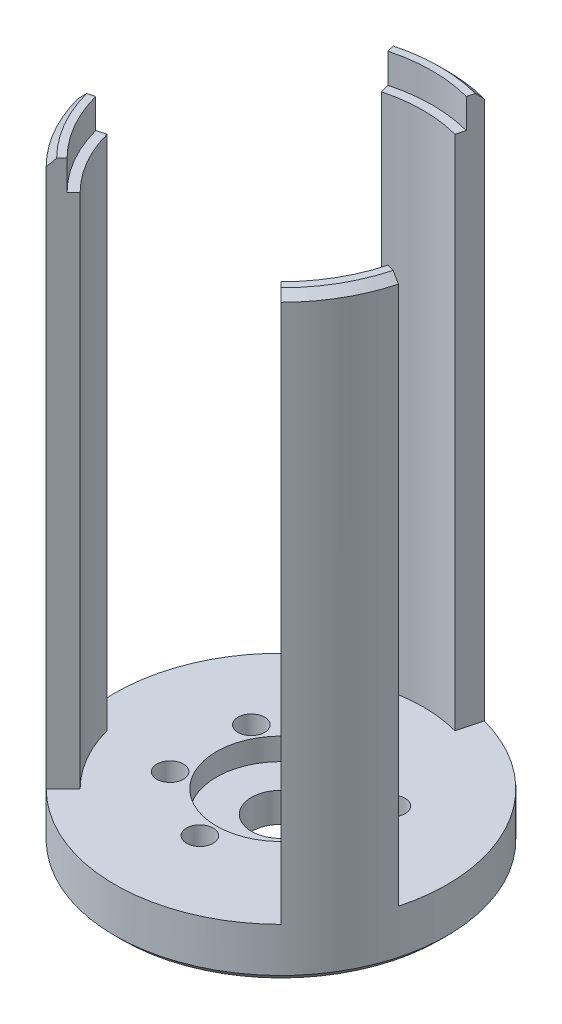
SolidWorks part; units mm, degrees
ref_plane "Front Plane" through (0, 0, 0) normal (0, 0, 1) x (1, 0, 0)
ref_plane "Top Plane" through (0, 0, 0) normal (0, 1, 0) x (1, 0, 0)
ref_plane "Right Plane" through (0, 0, 0) normal (1, 0, 0) x (0, 0, -1)
sketch "Sketch1" plane through (0, 0, 0) normal (0, 1, 0) x (1, 0, 0)
  line L0 (0, 0) -> (0, 11) construction
  line L1 (0, 0) -> (9.5263, 5.5) construction
  circle A0 centre (0, 0) radius 22.5
  circle A1 centre (0, 0) radius 11 construction
  circle A2 centre (0, 11) radius 1.8
  circle A3 centre (9.5263, 5.5) radius 1.8
  circle A4 centre (9.5263, -5.5) radius 1.8
  circle A5 centre (0, -11) radius 1.8
  circle A6 centre (-9.5263, -5.5) radius 1.8
  circle A7 centre (-9.5263, 5.5) radius 1.8
  circle A8 centre (0, 0) radius 4
  dimension "D1" = 45
  dimension "D2" = 22
  dimension "D3" = 3.6
  dimension "D5" = 8
  dimension "D4" = 60
extrude "Boss-Extrude1" add sketch "Sketch1" along normal blind 7
sketch "Sketch4" plane through (0, 7, 0) normal (0, 1, 0) x (1, 0, 0)
  circle A0 centre (0, 0) radius 8.75
  dimension "D1" = 17.5
extrude "Cut-Extrude2" cut sketch "Sketch4" against normal blind 3
sketch "Sketch6" plane through (0, 0, 0) normal (0, -1, 0) x (1, 0, 0)
  circle A0 centre (0, 11) radius 3.25
  circle A1 centre (9.5263, -5.5) radius 3.25
  circle A2 centre (-9.5263, -5.5) radius 3.25
  point P9 (0, 0)
  dimension "D1" = 6.5
  dimension "D2" = 3
extrude "Cut-Extrude3" cut sketch "Sketch6" against normal blind 2.5
sketch "Sketch2" plane through (0, 7, 0) normal (0, 1, 0) x (1, 0, 0)
  line L0 (0, 0) -> (0, 22.5) construction
  line L1 (0, 0) -> (9.5263, -5.5) construction
  line L2 (9.5263, -5.5) -> (19.4856, -11.25) construction
  line L3 (0, 0) -> (-9.5263, -5.5) construction
  line L4 (-9.5263, -5.5) -> (-19.4856, -11.25) construction
  line L5 (4.9823, 18.5941) -> (5.8234, 21.7333)
  line L6 (-4.9823, 18.5941) -> (-5.8234, 21.7333)
  line L7 (18.5941, -4.9823) -> (21.7333, -5.8234)
  line L8 (13.6118, -13.6118) -> (15.9099, -15.9099)
  line L9 (-13.6118, -13.6118) -> (-15.9099, -15.9099)
  line L10 (-18.5941, -4.9823) -> (-21.7333, -5.8234)
  circle A0 centre (0, 0) radius 22.5 construction
  arc A2 (15.9099, -15.9099) -> (21.7333, -5.8234) centre (0, 0) ccw
  arc A4 (5.8234, 21.7333) -> (-5.8234, 21.7333) centre (0, 0) ccw
  arc A5 (4.9823, 18.5941) -> (-4.9823, 18.5941) centre (0, 0) ccw
  arc A6 (13.6118, -13.6118) -> (18.5941, -4.9823) centre (0, 0) ccw
  arc A7 (-21.7333, -5.8234) -> (-15.9099, -15.9099) centre (0, 0) ccw
  arc A8 (-18.5941, -4.9823) -> (-13.6118, -13.6118) centre (0, 0) ccw
  point P26 (0, 0)
  dimension "D1" = 19.25
  dimension "D2" = 15
  dimension "D3" = 3
extrude "Boss-Extrude2" add sketch "Sketch2" along normal blind 74
sketch "Sketch7" plane through (0, 81, 0) normal (0, 1, 0) x (1, 0, 0)
  circle A0 centre (0, 0) radius 20.5
  dimension "D1" = 41
extrude "Cut-Extrude4" cut sketch "Sketch7" against normal blind 4
chamfer "Chamfer2" distance 1 angle 45 4 edges at (0, 81, -22.5) (19.4856, 81, 11.25) (-19.4856, 81, 11.25) (0, 0, 22.5)
